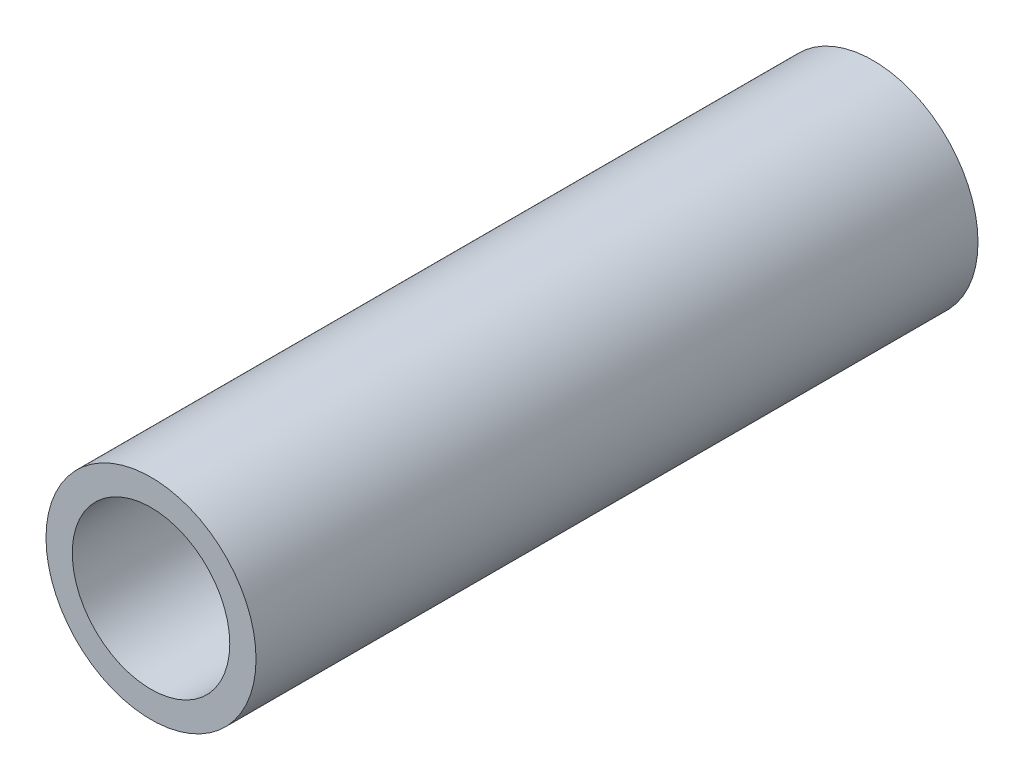
SolidWorks part; units mm, degrees
material "亚克力"
ref_plane "前视基准面" through (0, 0, 0) normal (0, 0, 1) x (1, 0, 0)
ref_plane "上视基准面" through (0, 0, 0) normal (0, 1, 0) x (1, 0, 0)
ref_plane "右视基准面" through (0, 0, 0) normal (1, 0, 0) x (0, 0, -1)
sketch "草图1" plane through (0, 0, 0) normal (0, 0, 1) x (1, 0, 0)
  circle A0 centre (0, 0) radius 6
  circle A1 centre (0, 0) radius 8
  dimension "D1" = 12
  dimension "D2" = 16
extrude "凸台-拉伸1" add sketch "草图1" along normal blind 55
